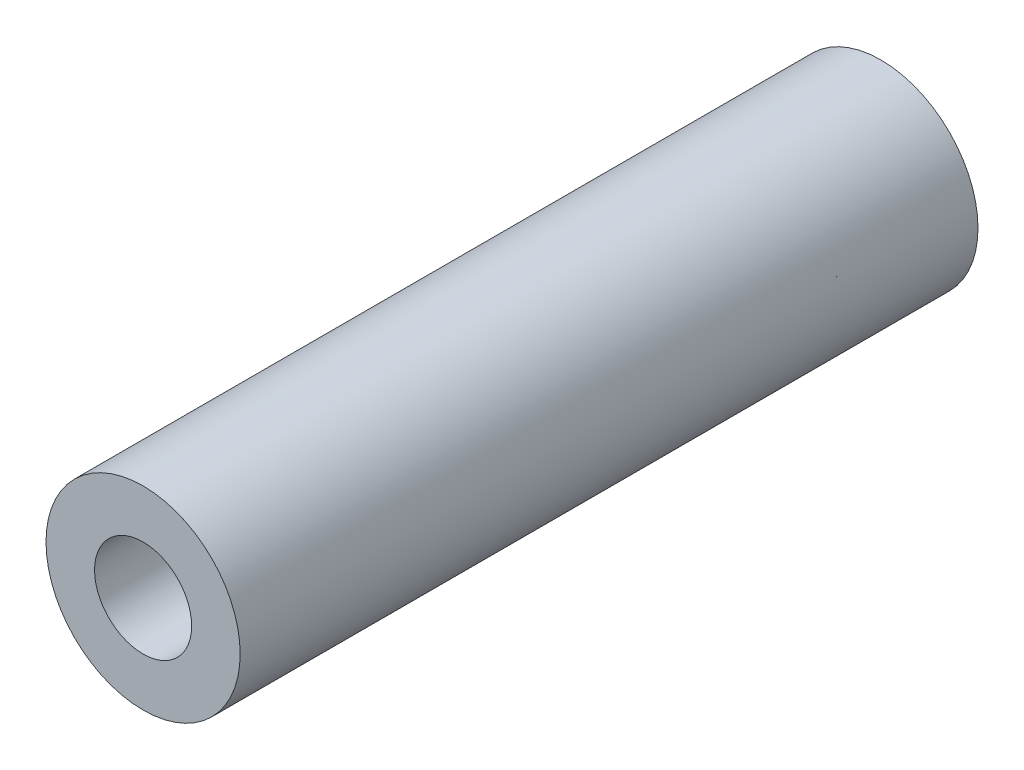
SolidWorks part; units mm, degrees
ref_plane "正面" through (0, 0, 0) normal (0, 0, 1) x (1, 0, 0)
ref_plane "平面" through (0, 0, 0) normal (0, 1, 0) x (1, 0, 0)
ref_plane "右側面" through (0, 0, 0) normal (1, 0, 0) x (0, 0, -1)
sketch "ｽｹｯﾁ1" plane through (0, 0, 0) normal (0, 0, 1) x (1, 0, 0)
  circle A0 centre (0, 0) radius 2.5
  dimension "D1" = 5
extrude "ﾎﾞｽ - 押し出し1" add sketch "ｽｹｯﾁ1" along normal mid plane 19
hole_wizard "M3x0.5 ねじ穴1" positions "3Dｽｹｯﾁ1" profile "ｽｹｯﾁ2" tap size "M3x0.5" standard "JIS"
sketch3d "3Dｽｹｯﾁ1"
  line L0 (0, 0, 9.5) -> (0, 0, -9.5) construction
  point P0 (0, 0, 9.5)
  point P4 (0, 0, -9.5)
sketch "ｽｹｯﾁ2" plane through (0, 0, 9.5) normal (1, 0, 0) x (0, -1, 0)
  line L0 (0, 0) -> (0, 9.2511)
  line L1 (0, 9.2511) -> (1.25, 8.5)
  line L2 (1.25, 8.5) -> (1.25, 0)
  line L5 (1.25, 0) -> (0, 0)
  line L10 (0, 9.2511) -> (-1.25, 8.5) construction
  line L11 (0, -6.35) -> (0, 107.95) construction
  dimension "ねじ下穴ﾄﾞﾘﾙ直径" = 2.5
  dimension "ねじ下穴ﾄﾞﾘﾙの深さ" = 8.5
  dimension "ﾄﾞﾘﾙ角度" = 118
cosmetic thread "穴のねじ山1" parameters "D1"=6, "D2"=3
cosmetic thread "穴のねじ山2" parameters "D1"=6, "D2"=3
sketch "ｽｹｯﾁ3" plane through (0, 0, -9.5) normal (0, 0, -1) x (-1, 0, 0)
  circle A0 centre (0, 0) radius 1.25
extrude "ｶｯﾄ - 押し出し1" cut sketch "ｽｹｯﾁ3" against normal blind 19
